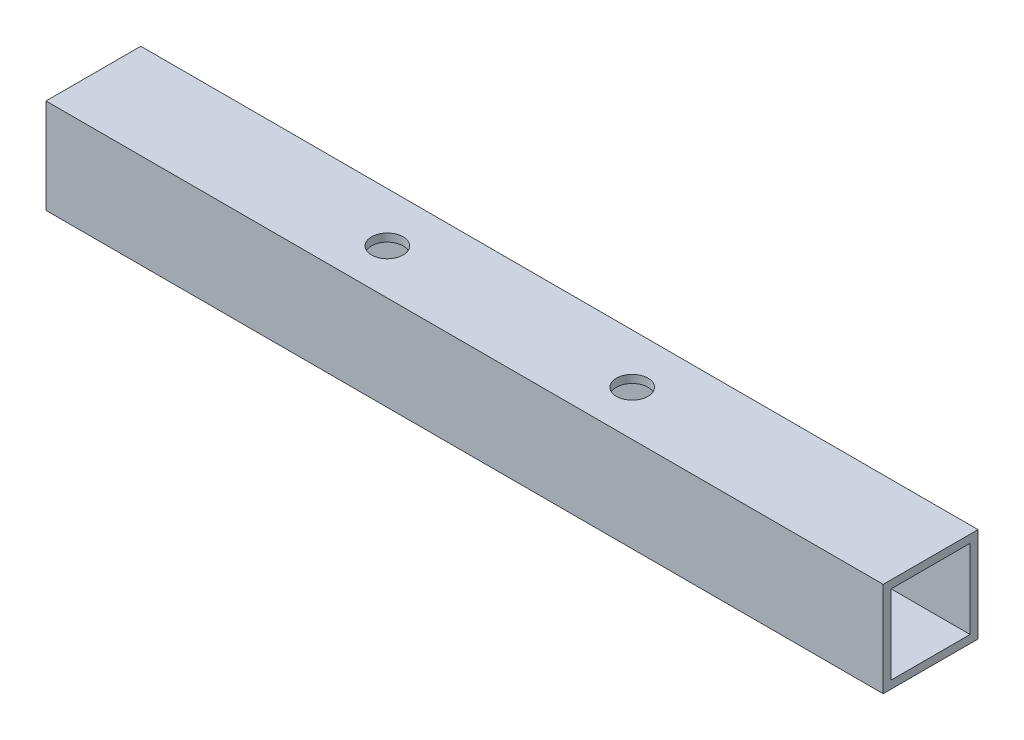
SolidWorks part; units mm, degrees
ref_plane "Front Plane" through (0, 0, 0) normal (0, 0, 1) x (1, 0, 0)
ref_plane "Top Plane" through (0, 0, 0) normal (0, 1, 0) x (1, 0, 0)
ref_plane "Right Plane" through (0, 0, 0) normal (1, 0, 0) x (0, 0, -1)
sketch "Sketch1" plane through (0, 0, 0) normal (0, 0, 1) x (1, 0, 0)
  line L1 (-53, -6) -> (53, -6)
  line L2 (-53, -6) -> (-53, 6)
  line L3 (-53, 6) -> (53, 6)
  line L4 (53, -6) -> (53, 6)
  line L5 (-53, -6) -> (53, 6) construction
  line L6 (-53, 6) -> (53, -6) construction
  point P0 (0, 0)
  dimension "D1" = 12
  dimension "D2" = 106
extrude "Boss-Extrude1" add sketch "Sketch1" along normal blind 12
sketch "Sketch2" plane through (0, 6, 0) normal (0, 1, 0) x (1, 0, 0)
  line L0 (-53, -12) -> (-53, 0) construction
  line L1 (0, 14.492) -> (0, -25.1371) construction
  circle A0 centre (-15.5, -6.2823) radius 2
  circle A1 centre (15.5, -6.2823) radius 2
  dimension "D1" = 4
  dimension "D2" = 37.5
extrude "Cut-Extrude1" cut sketch "Sketch2" against normal blind 12
sketch "Sketch3" plane through (53, 0, 0) normal (1, 0, 0) x (0, 0, -1)
  line L0 (-12, 6) -> (0, 6) construction
  line L1 (-11, 5) -> (-1, 5)
  line L2 (-11, 5) -> (-11, -5)
  line L3 (-11, -5) -> (-1, -5)
  line L4 (-1, 5) -> (-1, -5)
  line L5 (-11, 5) -> (-1, -5) construction
  line L6 (-11, -5) -> (-1, 5) construction
  line L7 (0, -6) -> (0, 6) construction
  line L8 (-12, -6) -> (-12, 6) construction
  line L9 (-12, -6) -> (0, -6) construction
  point P0 (-6, 0)
  dimension "D1" = 1
  dimension "D2" = 1
  dimension "D3" = 1
  dimension "D4" = 1
extrude "Cut-Extrude2" cut sketch "Sketch3" against normal blind 128
